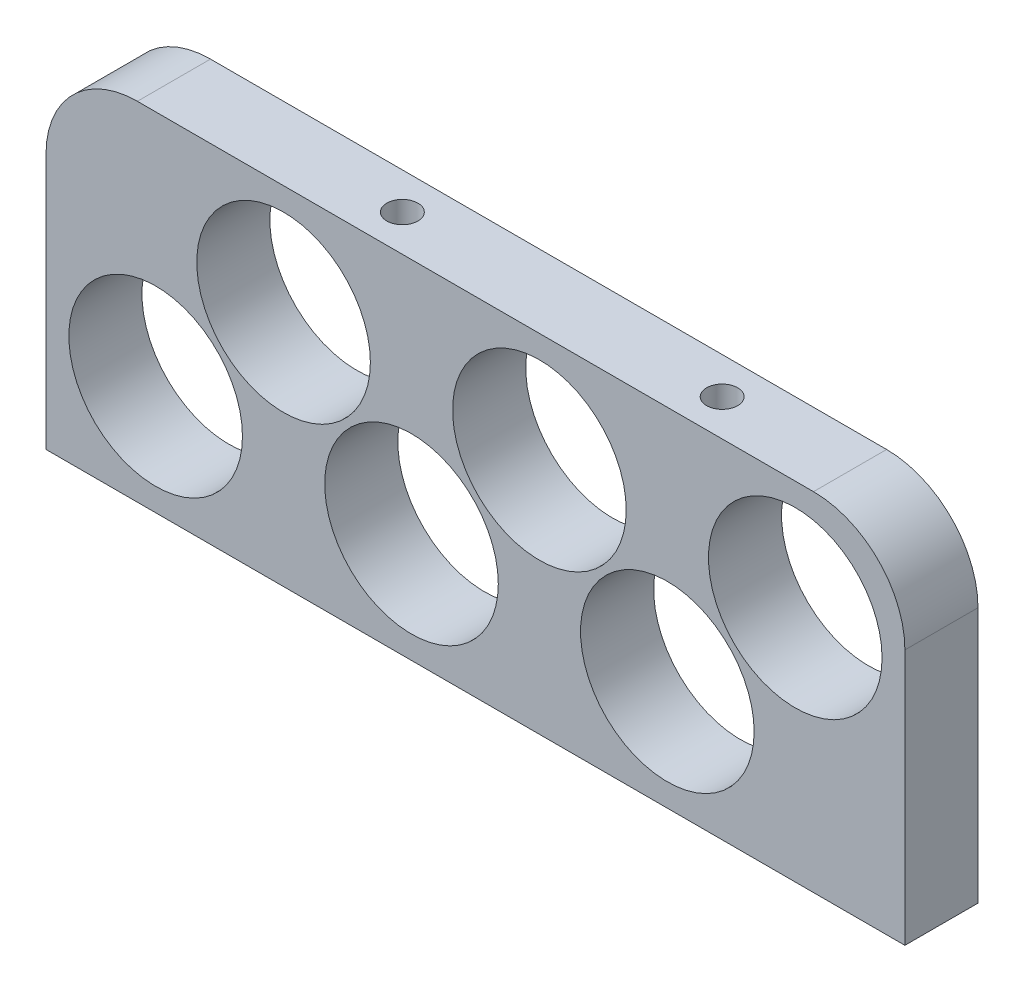
SolidWorks part; units mm, degrees
ref_plane "Płaszczyzna przednia" through (0, 0, 0) normal (0, 0, 1) x (1, 0, 0)
ref_plane "Płaszczyzna górna" through (0, 0, 0) normal (0, 1, 0) x (1, 0, 0)
ref_plane "Płaszczyzna prawa" through (0, 0, 0) normal (1, 0, 0) x (0, 0, -1)
sketch "Sketch2" plane through (0, 0, 0) normal (0, 0, 1) x (1, 0, 0)
  line L1 (-198.8216, 39.9918) -> (-104.8216, 39.9918)
  line L2 (-198.8216, 39.9918) -> (-198.8216, 1.9918)
  line L3 (-198.8216, 1.9918) -> (-104.8216, 1.9918)
  line L4 (-104.8216, 39.9918) -> (-104.8216, 1.9918)
  circle A0 centre (-186.8216, 13.9918) radius 9.5
  circle A1 centre (-158.8216, 13.9918) radius 9.5
  circle A2 centre (-130.8216, 13.9918) radius 9.5
  circle A3 centre (-144.8216, 27.9918) radius 9.5
  circle A4 centre (-116.8216, 27.9918) radius 9.5
  circle A5 centre (-172.8216, 27.9918) radius 9.5
  dimension "D5" = 19
  dimension "D1" = 12
  dimension "D2" = 12
  dimension "D3" = 12
  dimension "D4" = 12
  dimension "D8" = 28
  dimension "D9" = 19.799
  dimension "D6" = 3
  dimension "D7" = 2
extrude "Boss-Extrude1" add sketch "Sketch2" along normal blind 8
fillet "Fillet1" radius 10 2 edges at (-104.8216, 39.9918, 4) (-198.8216, 39.9918, 4)
sketch "Sketch3" plane through (0, 39.9918, 0) normal (0, 1, 0) x (1, 0, 0)
  line L0 (-114.8216, 0) -> (-188.8216, 0) construction
  line L2 (-114.8216, -8) -> (-114.8216, 0) construction
  circle A0 centre (-163.8216, -4) radius 1.7
  circle A1 centre (-128.8216, -4) radius 1.7
  dimension "D1" = 3.4
  dimension "D2" = 4
  dimension "D3" = 4
  dimension "D4" = 35
  dimension "D5" = 14
extrude "Cut-Extrude1" cut sketch "Sketch3" against normal blind 5
